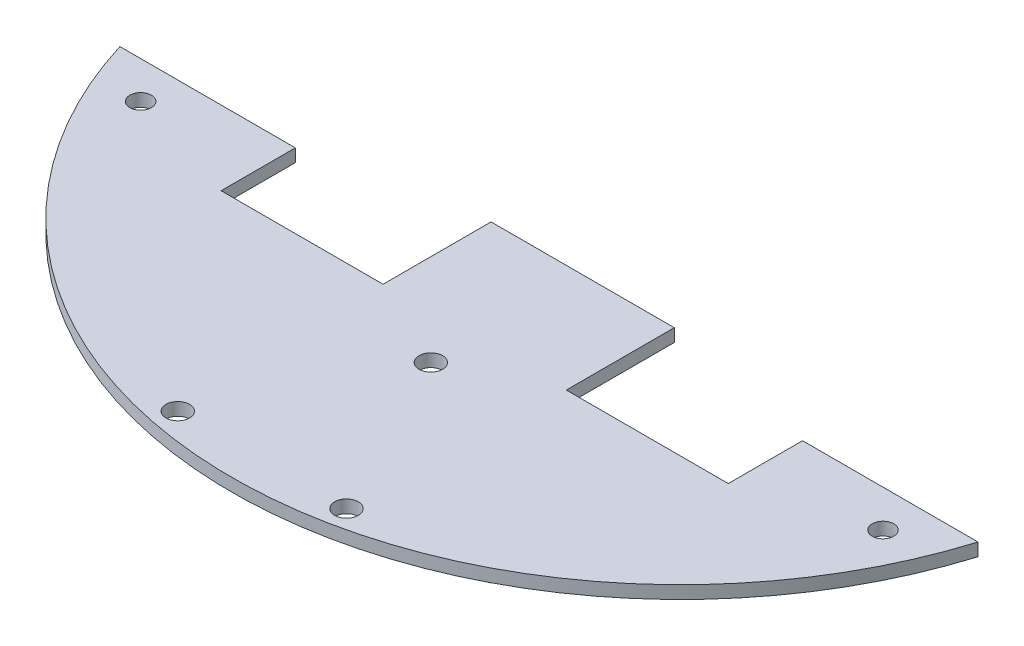
SolidWorks part; units mm, degrees
material "ABS"
ref_plane "Front Plane" through (0, 0, 0) normal (0, 0, 1) x (1, 0, 0)
ref_plane "Top Plane" through (0, 0, 0) normal (0, 1, 0) x (1, 0, 0)
ref_plane "Right Plane" through (0, 0, 0) normal (1, 0, 0) x (0, 0, -1)
sketch "Sketch1" plane through (0, 0, 0) normal (0, 1, 0) x (1, 0, 0)
  line L1 (-18, -10) -> (18, -10)
  line L2 (-18, -10) -> (-18, 10)
  line L3 (-18, 10) -> (18, 10)
  line L4 (18, -10) -> (18, 10)
  line L5 (-18, -10) -> (18, 10) construction
  line L6 (-18, 10) -> (18, -10) construction
  point P0 (0, 0)
  dimension "D1" = 36
  dimension "D2" = 20
extrude "Boss-Extrude1" add sketch "Sketch1" along normal blind 1.9
sketch "Sketch2" plane through (0, 0, 0) normal (0, -1, 0) x (1, 0, 0)
  line L0 (0, -10) -> (0, 10) construction
  line L1 (18, -10) -> (-18, -10) construction
  line L2 (-18, 10) -> (18, 10) construction
sketch "Sketch3" plane through (0, 0, 0) normal (0, -1, 0) x (1, 0, 0)
  line L0 (0, 0) -> (0, 56.5743) construction
  line L1 (-37.5767, 45.5743) -> (-37.5767, 56.5743)
  line L2 (-37.5767, 56.5743) -> (-13.5767, 56.5743)
  line L3 (0, 0) -> (0, -36.2287) construction
  line L4 (-13.5767, 56.5743) -> (-13.5767, 40.5743)
  line L5 (-13.5767, 40.5743) -> (13.5767, 40.5743)
  line L6 (13.5767, 40.5743) -> (13.5767, 56.5743)
  line L7 (37.5767, 45.5743) -> (63.5767, 45.5743)
  line L8 (13.5767, 56.5743) -> (37.5767, 56.5743)
  line L9 (-37.5767, 45.5743) -> (-63.5767, 45.5743)
  line L10 (37.5767, 56.5743) -> (37.5767, 45.5743)
  arc A2 (68.1909, 19.5743) -> (-68.1909, 19.5743) centre (0, 26.0743) ccw construction
  arc A3 (63.5767, 45.5743) -> (-63.5767, 45.5743) centre (0, 26.0743) ccw
  circle A4 centre (0, 26.0743) radius 72.5 construction
  point P14 (-25.5767, 56.5743)
  point P20 (-63.5767, 45.5743)
  point P26 (63.5767, 45.5743)
  dimension "D1" = 2
  dimension "D3" = 5
  dimension "D4" = 52
  dimension "D5" = 26
  dimension "D6" = 16
  dimension "D2" = 24
extrude "Boss-Extrude2" add sketch "Sketch3" against normal blind 1.9
sketch "Sketch5" plane through (0, 1.9, 0) normal (0, 1, 0) x (1, 0, 0)
  line L2 (-29.6163, 16.0438) -> (29.6163, 16.0438)
  line L3 (-29.6163, 16.0438) -> (-29.6163, -16.0438)
  line L4 (-29.6163, -16.0438) -> (29.6163, -16.0438)
  line L5 (29.6163, 16.0438) -> (29.6163, -16.0438)
  line L6 (-29.6163, 16.0438) -> (29.6163, -16.0438) construction
  line L7 (-29.6163, -16.0438) -> (29.6163, 16.0438) construction
extrude "Cut-Extrude2" cut sketch "Sketch5" against normal blind 10
sketch "Sketch8" plane through (0, 1.9, 0) normal (0, 1, 0) x (1, 0, 0)
  line L0 (0, -26.0743) -> (-47.0226, -73.0969) construction
  line L1 (0, -26.0743) -> (0, -92.5743) construction
  line L2 (0, -26.0743) -> (-25.4484, -87.5123) construction
  line L3 (-63.5767, -45.5743) -> (-37.5767, -45.5743) construction
  line L4 (0, -26.0743) -> (47.0226, -73.0969) construction
  line L5 (0, -26.0743) -> (25.4484, -87.5123) construction
  circle A0 centre (0, -26.0743) radius 66.5 construction
  arc A1 (-63.5767, -45.5743) -> (63.5767, -45.5743) centre (0, -26.0743) ccw construction
  dimension "D1" = 45
  dimension "D2" = 67.5
sketch "Sketch9" plane through (0, 1.9, 0) normal (0, 1, 0) x (1, 0, 0)
  line L0 (18.5, -61.5743) -> (11.5, -61.5743)
  line L1 (18.5, -61.5743) -> (18.5, -73.5743)
  line L2 (18.5, -73.5743) -> (11.5, -73.5743)
  line L3 (11.5, -61.5743) -> (11.5, -73.5743)
  line L4 (-11.5, -61.5743) -> (-11.5, -73.5743)
  line L5 (-18.5, -73.5743) -> (-11.5, -73.5743)
  line L6 (-18.5, -61.5743) -> (-18.5, -73.5743)
  line L7 (-18.5, -61.5743) -> (-11.5, -61.5743)
  line L8 (-15, -61.5743) -> (-15, -73.5743) construction
  line L9 (15, -61.5743) -> (15, -73.5743) construction
  line L11 (-15, -67.5743) -> (15, -67.5743) construction
  line L12 (0, -26.0743) -> (0, -92.5743) construction
  line L13 (-18.5, -61.5743) -> (18.5, -61.5743) construction
  line L15 (-18.5, -61.5743) -> (-11.5, -73.5743)
  line L16 (-18.5, -73.5743) -> (-11.5, -61.5743)
  line L17 (11.5, -61.5743) -> (18.5, -73.5743)
  line L18 (18.5, -61.5743) -> (11.5, -73.5743)
  point P17 (0, -67.5743)
  point P28 (-15, -67.5743)
  point P29 (15, -67.5743)
  dimension "D1" = 7
  dimension "D2" = 12
  dimension "D3" = 30
  dimension "D7" = 25
sketch "Sketch10" plane through (0, 1.9, 0) normal (0, 1, 0) x (1, 0, 0)
  line L0 (-12.5, -88.0743) -> (12.5, -88.0743) construction
  line L1 (-13.5767, -40.5743) -> (13.5767, -40.5743) construction
  line L2 (0, -26.0743) -> (0, -92.5743) construction
  circle A0 centre (-12.5, -88.0743) radius 1.75
  circle A1 centre (12.5, -88.0743) radius 1.75
  circle A2 centre (0, -63.0743) radius 1.75
  point P6 (0, -88.0743)
  dimension "D1" = 25
  dimension "D3" = 3.5
  dimension "D4" = 25
  dimension "D2" = 47.5
extrude "Cut-Extrude3" cut sketch "Sketch10" against normal blind 10
sketch "Sketch11" plane through (0, 0, 0) normal (0, -1, 0) x (1, 0, 0)
  line L0 (-37.5767, 45.5743) -> (-37.5767, 56.5743) construction
  line L1 (-63.5767, 45.5743) -> (-37.5767, 45.5743) construction
  line L2 (-55, 51.0743) -> (55, 51.0743) construction
  line L3 (37.5767, 56.5743) -> (37.5767, 45.5743) construction
  circle A0 centre (-55, 51.0743) radius 1.6
  circle A2 centre (55, 51.0743) radius 1.6
  dimension "D1" = 5.5
  dimension "D2" = 3.2
  dimension "D3" = 17.4233
  dimension "D4" = 17.4233
extrude "Cut-Extrude4" cut sketch "Sketch11" against normal blind 4
